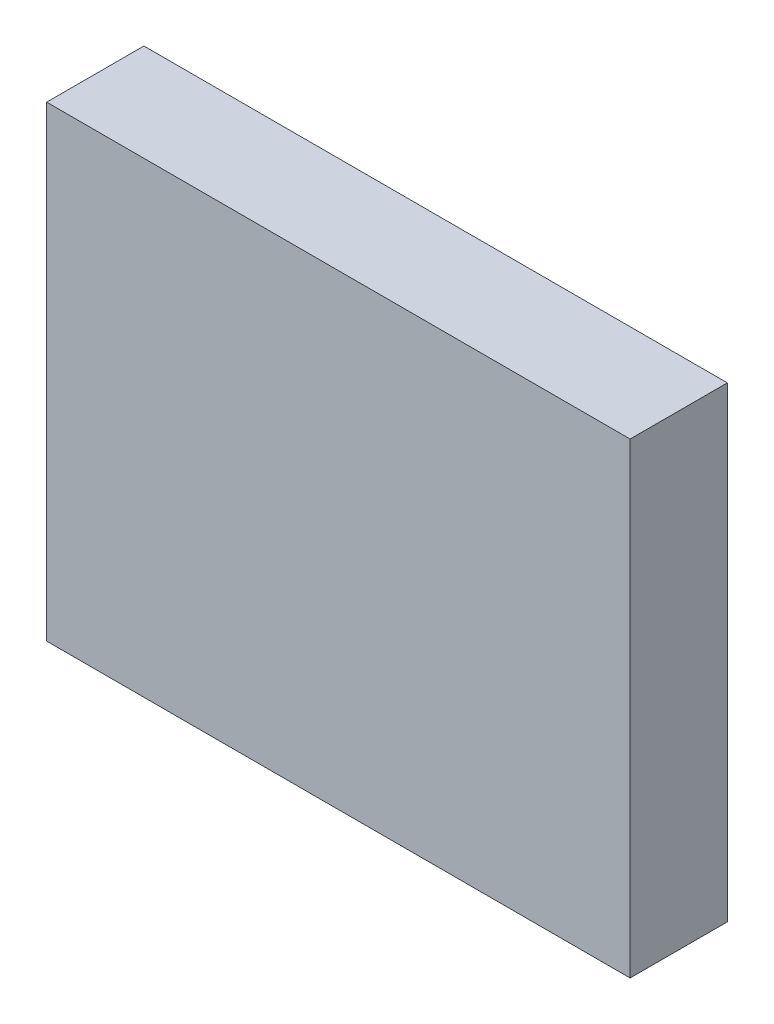
SolidWorks part; units mm, degrees
ref_plane "Plan de face" through (0, 0, 0) normal (0, 0, 1) x (1, 0, 0)
ref_plane "Plan de dessus" through (0, 0, 0) normal (0, 1, 0) x (1, 0, 0)
ref_plane "Plan de droite" through (0, 0, 0) normal (1, 0, 0) x (0, 0, -1)
sketch "Esquisse1" plane through (0, 0, 0) normal (0, 0, 1) x (1, 0, 0)
  line L1 (-9.1605, 13.2149) -> (20.8395, 13.2149)
  line L2 (-9.1605, 13.2149) -> (-9.1605, -10.7851)
  line L3 (-9.1605, -10.7851) -> (20.8395, -10.7851)
  line L4 (20.8395, 13.2149) -> (20.8395, -10.7851)
  dimension "D1" = 30
  dimension "D2" = 24
extrude "Boss.-Extru.1" add sketch "Esquisse1" along normal blind 5
